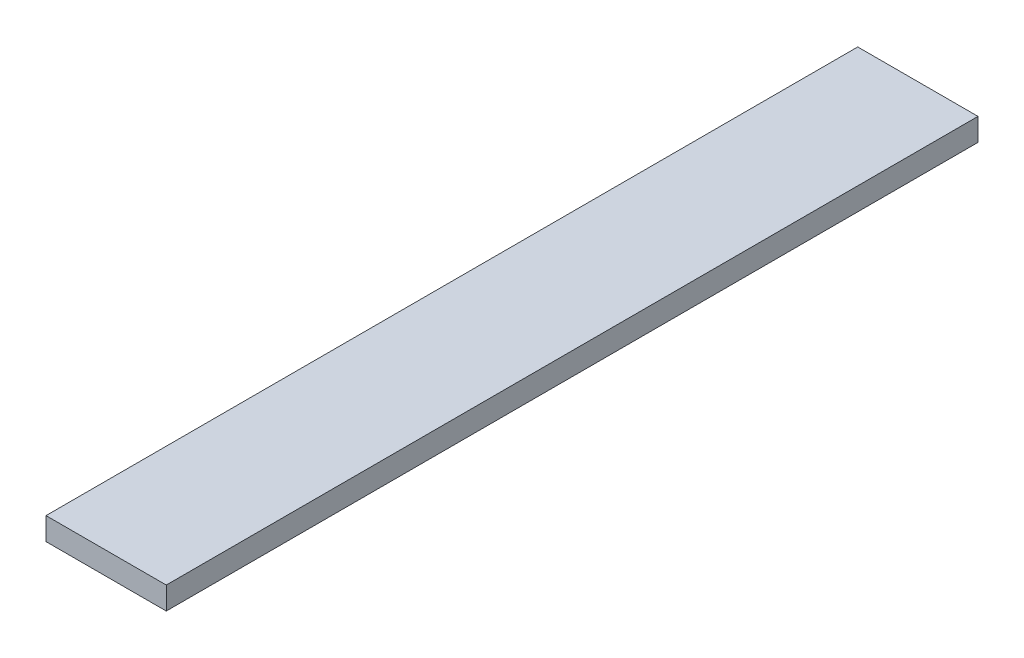
SolidWorks part; units mm, degrees
material "Pine"
ref_plane "Front Plane" through (0, 0, 0) normal (0, 0, 1) x (1, 0, 0)
ref_plane "Top Plane" through (0, 0, 0) normal (0, 1, 0) x (1, 0, 0)
ref_plane "Right Plane" through (0, 0, 0) normal (1, 0, 0) x (0, 0, -1)
sketch "Sketch1" plane through (0, 0, 0) normal (0, 1, 0) x (1, 0, 0)
  line L1 (-50.8, 342.9) -> (50.8, 342.9)
  line L2 (-50.8, 342.9) -> (-50.8, -342.9)
  line L3 (-50.8, -342.9) -> (50.8, -342.9)
  line L4 (50.8, 342.9) -> (50.8, -342.9)
  line L5 (-50.8, 342.9) -> (50.8, -342.9) construction
  line L6 (-50.8, -342.9) -> (50.8, 342.9) construction
  point P0 (0, 0)
  dimension "D1" = 685.8
  dimension "D2" = 101.6
extrude "Boss-Extrude1" add sketch "Sketch1" along normal blind 19.05
